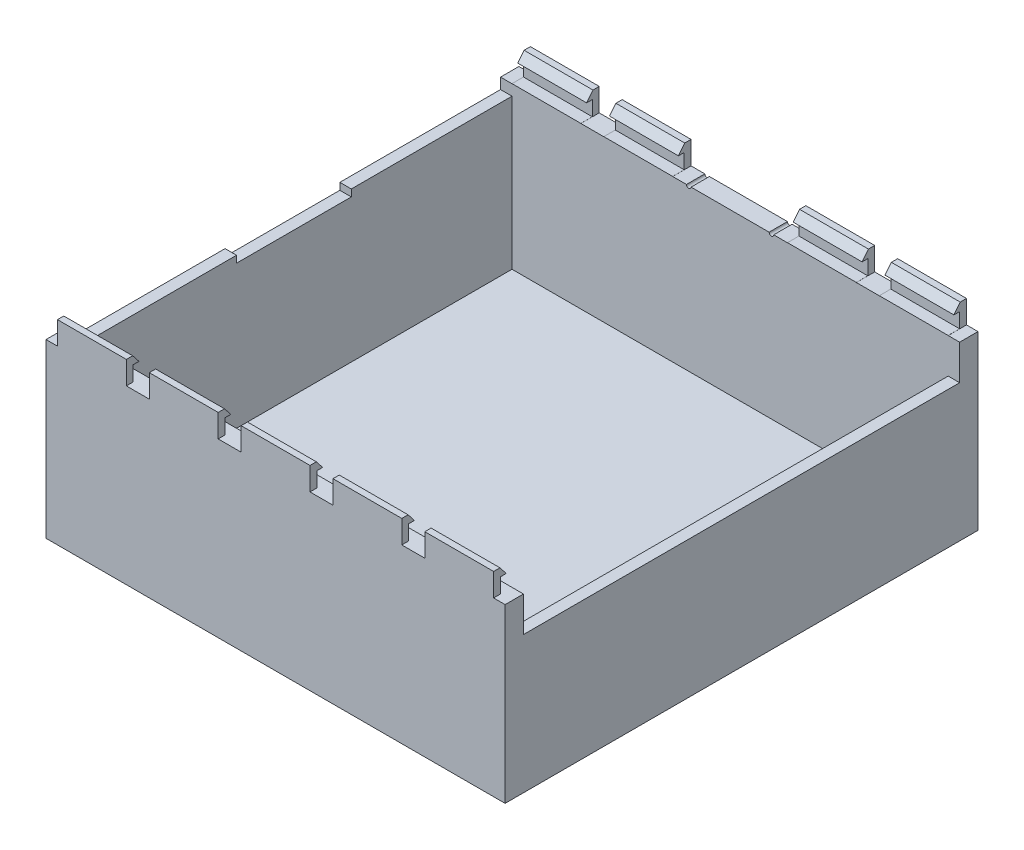
SolidWorks part; units mm, degrees
ref_plane "Спереди" through (0, 0, 0) normal (0, 0, 1) x (1, 0, 0)
ref_plane "Сверху" through (0, 0, 0) normal (0, 1, 0) x (1, 0, 0)
ref_plane "Справа" through (0, 0, 0) normal (1, 0, 0) x (0, 0, -1)
sketch "Эскиз1" plane through (0, 0, 0) normal (0, 1, 0) x (1, 0, 0)
  line L1 (100, -103) -> (-100, -103)
  line L2 (100, -103) -> (100, 103)
  line L3 (100, 103) -> (-100, 103)
  line L4 (-100, -103) -> (-100, 103)
  line L5 (100, -103) -> (-100, 103) construction
  line L6 (100, 103) -> (-100, -103) construction
  point P0 (0, 0)
  dimension "D1" = 200
  dimension "D2" = 206
extrude "Бобышка-Вытянуть2" add sketch "Эскиз1" along normal blind 5
sketch "Эскиз2" plane through (0, 5, 0) normal (0, 1, 0) x (1, 0, 0)
  line L0 (100, -103) -> (100, 103) construction
  line L1 (-100, -103) -> (100, -103)
  line L2 (-100, -103) -> (-100, -95)
  line L3 (-100, -95) -> (100, -95)
  line L4 (100, -103) -> (100, -95)
  point P7 (100, -99)
  dimension "D1" = 4
extrude "Бобышка-Вытянуть3" add sketch "Эскиз2" along normal blind 70
sketch "Эскиз3" plane through (0, 5, 0) normal (0, 1, 0) x (1, 0, 0)
  line L2 (100, -95) -> (95, -95)
  line L3 (100, -95) -> (100, 95)
  line L4 (100, 95) -> (95, 95)
  line L5 (95, -95) -> (95, 95)
  dimension "D1" = 190
  dimension "D2" = 5
extrude "Бобышка-Вытянуть4" add sketch "Эскиз3" along normal blind 54.7
sketch "Эскиз4" plane through (0, 5, 0) normal (0, 1, 0) x (1, 0, 0)
  line L2 (100, 95) -> (-100, 95)
  line L3 (100, 95) -> (100, 103)
  line L4 (100, 103) -> (-100, 103)
  line L5 (-100, 95) -> (-100, 103)
  dimension "D1" = 8
extrude "Бобышка-Вытянуть5" add sketch "Эскиз4" along normal blind 70
sketch "Эскиз14" plane through (0, 5, 0) normal (0, 1, 0) x (1, 0, 0)
  line L1 (-100, -95) -> (-95, -95)
  line L2 (-100, -95) -> (-100, 95)
  line L3 (-100, 95) -> (-95, 95)
  line L4 (-95, -95) -> (-95, 95)
  dimension "D1" = 5
extrude "Бобышка-Вытянуть7" add sketch "Эскиз14" along normal blind 65.3
sketch "Эскиз15" plane through (0, 70.3, 0) normal (0, 1, 0) x (1, 0, 0)
  line L0 (-95, -95) -> (-95, 95) construction
  line L1 (-95, 0) -> (-100, 0) construction
  line L2 (-100, 95) -> (-100, -95) construction
  line L4 (-100, -25) -> (-95, -25)
  line L5 (-100, -25) -> (-100, 25)
  line L6 (-100, 25) -> (-95, 25)
  line L7 (-95, -25) -> (-95, 25)
  line L8 (-100, -25) -> (-95, 25) construction
  line L9 (-100, 25) -> (-95, -25) construction
  point P6 (-97.5, 0)
  dimension "D1" = 50
extrude "Вырез-Вытянуть7" cut sketch "Эскиз15" against normal blind 3
sketch "Эскиз16" plane through (0, 0, -103) normal (0, 0, -1) x (-1, 0, 0)
  line L0 (-100, 75) -> (100, 75) construction
  line L1 (0, 75) -> (-18, 75) construction
  arc A0 (-19, 75) -> (-17, 75) centre (-18, 75) ccw
  dimension "D1" = 18
  dimension "D3" = 1
extrude "Вырез-Вытянуть8" cut sketch "Эскиз16" against normal blind 8 and the other way through all
sketch "Эскиз18" plane through (0, 0, -103) normal (0, 0, -1) x (-1, 0, 0)
  line L0 (-17, 75) -> (18, 75) construction
  line L1 (-17, 75) -> (100, 75) construction
  arc A0 (17, 75) -> (19, 75) centre (18, 75) ccw
  dimension "D1" = 35
  dimension "D2" = 1
extrude "Вырез-Вытянуть9" cut sketch "Эскиз18" against normal blind 8 and the other way through all
sketch "Эскиз19" plane through (0, 0, -103) normal (0, 0, -1) x (-1, 0, 0)
  line L0 (0, 75) -> (0, 70) construction
  line L1 (-17, 75) -> (17, 75) construction
  circle A0 centre (0, 70) radius 1.5
  dimension "D2" = 3
  dimension "D1" = 5
extrude "Вырез-Вытянуть10" cut sketch "Эскиз19" against normal blind 5
sketch "Эскиз21" plane through (0, 75, 0) normal (0, 1, 0) x (1, 0, 0)
  line L0 (-100, -99) -> (-80, -99) construction
  line L1 (-100, -95) -> (-100, -103) construction
  line L2 (100, -95) -> (-100, -95) construction
  line L3 (-95, -103) -> (-65, -103)
  line L4 (-95, -103) -> (-95, -95)
  line L5 (-95, -95) -> (-65, -95)
  line L6 (-65, -103) -> (-65, -95)
  line L7 (-95, -103) -> (-65, -95) construction
  line L8 (-95, -95) -> (-65, -103) construction
  line L9 (-80, -99) -> (-40, -99) construction
  line L10 (-40, -99) -> (0, -99) construction
  line L11 (-55, -103) -> (-25, -103)
  line L12 (-55, -103) -> (-55, -95)
  line L13 (-55, -95) -> (-25, -95)
  line L14 (-25, -103) -> (-25, -95)
  line L15 (-55, -103) -> (-25, -95) construction
  line L16 (-55, -95) -> (-25, -103) construction
  line L17 (0, -99) -> (40, -99) construction
  line L18 (15, -103) -> (-15, -103)
  line L19 (15, -103) -> (15, -95)
  line L20 (15, -95) -> (-15, -95)
  line L21 (-15, -103) -> (-15, -95)
  line L22 (15, -103) -> (-15, -95) construction
  line L23 (15, -95) -> (-15, -103) construction
  line L24 (40, -99) -> (80, -99) construction
  line L25 (55, -103) -> (25, -103)
  line L26 (55, -103) -> (55, -95)
  line L27 (55, -95) -> (25, -95)
  line L28 (25, -103) -> (25, -95)
  line L29 (55, -103) -> (25, -95) construction
  line L30 (55, -95) -> (25, -103) construction
  line L31 (80, -99) -> (100, -99) construction
  line L32 (95, -103) -> (65, -103)
  line L33 (95, -103) -> (95, -95)
  line L34 (95, -95) -> (65, -95)
  line L35 (65, -103) -> (65, -95)
  line L36 (95, -103) -> (65, -95) construction
  line L37 (95, -95) -> (65, -103) construction
  line L38 (100, -103) -> (100, -95) construction
  line L39 (100, 99) -> (80, 99) construction
  line L40 (100, 95) -> (100, 103) construction
  line L41 (80, 99) -> (40, 99) construction
  line L42 (40, 99) -> (-40, 99) construction
  line L43 (-40, 99) -> (-80, 99) construction
  line L44 (-80, 99) -> (-100, 99) construction
  line L45 (-100, 103) -> (-100, 95) construction
  line L46 (19, 95) -> (100, 95) construction
  line L47 (65, 103) -> (95, 103)
  line L48 (65, 103) -> (65, 95)
  line L49 (65, 95) -> (95, 95)
  line L50 (95, 103) -> (95, 95)
  line L51 (65, 103) -> (95, 95) construction
  line L52 (65, 95) -> (95, 103) construction
  line L53 (-100, 95) -> (-19, 95) construction
  line L54 (25, 103) -> (55, 103)
  line L55 (25, 103) -> (25, 95)
  line L56 (25, 95) -> (55, 95)
  line L57 (55, 103) -> (55, 95)
  line L58 (25, 103) -> (55, 95) construction
  line L59 (25, 95) -> (55, 103) construction
  line L60 (-55, 103) -> (-25, 103)
  line L61 (-55, 103) -> (-55, 95)
  line L62 (-55, 95) -> (-25, 95)
  line L63 (-25, 103) -> (-25, 95)
  line L64 (-55, 103) -> (-25, 95) construction
  line L65 (-55, 95) -> (-25, 103) construction
  line L67 (-95, 103) -> (-65, 103)
  line L68 (-95, 103) -> (-95, 95)
  line L69 (-95, 95) -> (-65, 95)
  line L70 (-65, 103) -> (-65, 95)
  line L71 (-95, 103) -> (-65, 95) construction
  line L72 (-95, 95) -> (-65, 103) construction
  dimension "D1" = 20
  dimension "D2" = 30
  dimension "D3" = 40
  dimension "D4" = 30
  dimension "D5" = 40
  dimension "D6" = 30
  dimension "D7" = 40
  dimension "D8" = 30
  dimension "D9" = 40
  dimension "D10" = 30
  dimension "D11" = 20
  dimension "D12" = 40
  dimension "D13" = 20
  dimension "D14" = 40
  dimension "D15" = 20
  dimension "D16" = 30
  dimension "D17" = 30
  dimension "D18" = 30
  dimension "D19" = 30
extrude "Бобышка-Вытянуть8" add sketch "Эскиз21" along normal blind 10
sketch "Эскиз24" plane through (95, 0, 0) normal (1, 0, 0) x (0, 0, -1)
  line L1 (-95, 75) -> (-100, 75)
  line L2 (-95, 75) -> (-95, 81.5)
  line L3 (-95, 81.5) -> (-100, 81.5)
  line L4 (-100, 75) -> (-100, 81.5)
  dimension "D1" = 5
  dimension "D2" = 6.5
extrude "Вырез-Вытянуть11" cut sketch "Эскиз24" against normal through all
sketch "Эскиз25" plane through (95, 0, 0) normal (1, 0, 0) x (0, 0, -1)
  line L0 (-95, 81.5) -> (-100, 81.5) construction
  line L1 (-95, 85) -> (-97.5, 85)
  line L2 (-95, 85) -> (-95, 81.5)
  line L3 (-95, 81.5) -> (-97.5, 81.5)
  line L4 (-97.5, 85) -> (-97.5, 81.5)
  dimension "D1" = 2.5
extrude "Вырез-Вытянуть12" cut sketch "Эскиз25" against normal through all
sketch "Эскиз26" plane through (95, 0, 0) normal (1, 0, 0) x (0, 0, -1)
  line L0 (-97.5, 81.5) -> (-100.25, 85)
  line L1 (-103, 85) -> (-97.5, 85) construction
  line L2 (-100.25, 85) -> (-97.5, 85)
  line L3 (-97.5, 85) -> (-97.5, 81.5)
extrude "Вырез-Вытянуть13" cut sketch "Эскиз26" against normal through all
sketch "Эскиз27" plane through (95, 0, 0) normal (1, 0, 0) x (0, 0, -1)
  line L0 (95, 85) -> (95, 75) construction
  line L1 (95, 75.0325) -> (100, 75.0325)
  line L2 (95, 75.0325) -> (95, 81.5325)
  line L3 (95, 81.5325) -> (100, 81.5325)
  line L4 (100, 75.0325) -> (100, 81.5325)
  dimension "D1" = 6.5
  dimension "D2" = 5
extrude "Вырез-Вытянуть14" cut sketch "Эскиз27" against normal through all
sketch "Эскиз28" plane through (95, 0, 0) normal (1, 0, 0) x (0, 0, -1)
  line L0 (100, 81.5325) -> (95, 81.5325) construction
  line L1 (95, 85) -> (97.5, 85)
  line L2 (95, 85) -> (95, 81.5325)
  line L3 (95, 81.5325) -> (97.5, 81.5325)
  line L4 (97.5, 85) -> (97.5, 81.5325)
  dimension "D1" = 2.5
extrude "Вырез-Вытянуть15" cut sketch "Эскиз28" against normal through all
sketch "Эскиз29" plane through (95, 0, 0) normal (1, 0, 0) x (0, 0, -1)
  line L0 (97.5, 81.5325) -> (100.25, 85)
  line L1 (97.5, 85) -> (103, 85) construction
  line L2 (100.25, 85) -> (97.5, 85)
  line L3 (97.5, 85) -> (97.5, 81.5325)
extrude "Вырез-Вытянуть16" cut sketch "Эскиз29" against normal through all
